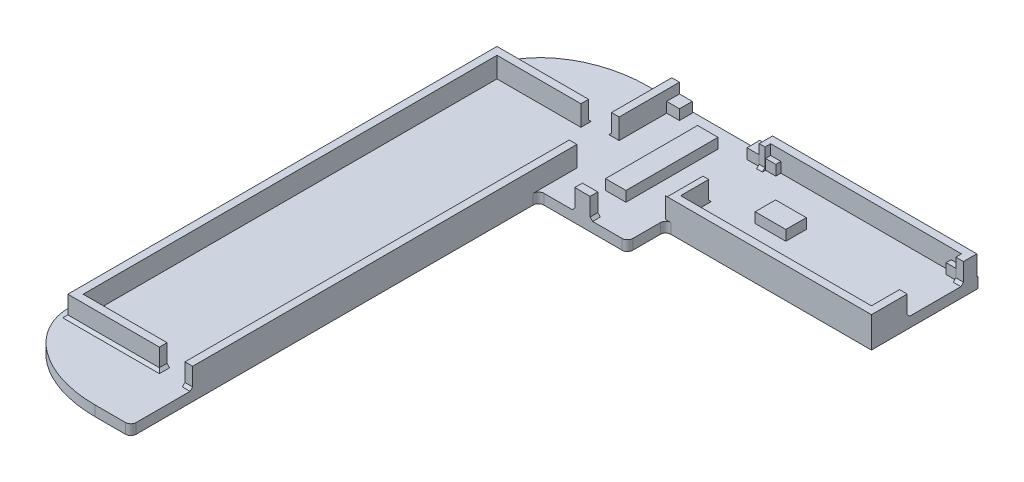
SolidWorks part; units mm, degrees
ref_plane "Front Plane" through (0, 0, 0) normal (0, 0, 1) x (1, 0, 0)
ref_plane "Top Plane" through (0, 0, 0) normal (0, 1, 0) x (1, 0, 0)
ref_plane "Right Plane" through (0, 0, 0) normal (1, 0, 0) x (0, 0, -1)
sketch "Sketch1" plane through (0, 0, 0) normal (0, 1, 0) x (1, 0, 0)
  line L0 (-57.0053, 40.4812) -> (-78.4053, 40.4812)
  line L1 (-78.4053, 40.4812) -> (-78.4053, -40.4188)
  line L2 (-78.4053, -40.4188) -> (-57.0053, -40.4188)
  line L3 (-57.0053, -40.4188) -> (-57.0053, 40.4812)
  line L4 (-78.1053, -40.1188) -> (-57.3053, -40.1188)
  line L5 (-57.3053, -40.1188) -> (-57.3053, 40.1812)
  line L6 (-57.3053, 40.1812) -> (-78.1053, 40.1812)
  line L7 (-78.1053, 40.1812) -> (-78.1053, -40.1188)
  line L8 (-78.1053, -40.1188) -> (-57.3053, -40.1188)
  line L9 (-57.3053, -40.1188) -> (-57.3053, 40.1812)
  line L10 (-57.3053, 40.1812) -> (-78.1053, 40.1812)
  line L11 (-78.1053, 40.1812) -> (-78.1053, -40.1188)
  line L12 (-55.5053, 41.9812) -> (-79.9053, 41.9812)
  line L13 (-79.9053, 41.9812) -> (-79.9053, -41.9188)
  line L14 (-79.9053, -41.9188) -> (-55.5053, -41.9188)
  line L15 (-55.5053, -41.9188) -> (-55.5053, 41.9812)
  line L16 (-56.0165, 54.3) -> (-56.0165, 33.2)
  line L17 (-48.4165, 27.2) -> (-45.4165, 27.2)
  line L18 (-37.8165, 33.2) -> (-37.8165, 40.1551)
  line L19 (-37.8165, 54.3) -> (-56.0165, 54.3)
  line L20 (-55.7165, 27.5) -> (-38.1165, 27.5)
  line L21 (-38.1165, 27.5) -> (-38.1165, 54)
  line L22 (-38.1165, 54) -> (-55.7165, 54)
  line L23 (-55.7165, 54) -> (-55.7165, 27.5)
  line L25 (-38.1165, 33.2) -> (-38.1165, 40.1551)
  line L26 (-38.1165, 54) -> (-55.7165, 54)
  line L27 (-55.7165, 54) -> (-55.7165, 33.2)
  line L28 (-36.3165, 55.8) -> (-57.5165, 55.8)
  line L29 (-57.5165, 55.8) -> (-57.5165, 33.2)
  line L30 (-48.4165, 25.7) -> (-45.4165, 25.7)
  line L31 (-36.3165, 33.2) -> (-36.3165, 34.9646)
  line L32 (-46.9165, 60.3419) -> (-46.9165, 21.4937) construction
  line L33 (-51.6665, 55.8) -> (-51.6665, 54.3)
  line L34 (-42.1665, 55.8) -> (-42.1665, 54.3)
  line L35 (0.6089, 52.2646) -> (-36.6911, 52.2646)
  line L36 (-36.6911, 52.2646) -> (-36.6911, 51.1551)
  line L37 (-36.6911, 34.6646) -> (0.6089, 34.6646)
  line L38 (0.6089, 34.6646) -> (0.6089, 40.1551)
  line L39 (0.3089, 34.9646) -> (0.3089, 51.9646)
  line L40 (0.3089, 51.9646) -> (-36.3911, 51.9646)
  line L41 (-36.3911, 51.9646) -> (-36.3911, 34.9646)
  line L42 (-36.3911, 34.9646) -> (0.3089, 34.9646)
  line L44 (0.3089, 51.9646) -> (-36.3911, 51.9646)
  line L46 (-36.3911, 34.9646) -> (0.3089, 34.9646)
  line L47 (2.1089, 53.7646) -> (-38.1911, 53.7646)
  line L48 (-38.1911, 53.7646) -> (-38.1911, 51.1551)
  line L49 (-38.1911, 33.1646) -> (2.1089, 33.1646)
  line L50 (2.1089, 33.1646) -> (2.1089, 40.1551)
  line L51 (0.6089, 51.1551) -> (2.1089, 51.1551)
  line L52 (7.7634, 45.6551) -> (-29.0417, 45.6551) construction
  line L53 (0.6089, 40.1551) -> (2.1089, 40.1551)
  line L54 (-18.0411, 53.7646) -> (-18.0411, 33.1646) construction
  line L55 (-36.6911, 40.1551) -> (-38.1911, 40.1551)
  line L56 (-36.6911, 51.1551) -> (-38.1911, 51.1551)
  line L57 (-57.5165, 33.2) -> (-36.3165, 33.2)
  line L58 (-48.4165, 27.2) -> (-48.4165, 25.7)
  line L59 (-45.4165, 27.2) -> (-45.4165, 25.7)
  line L60 (-55.7165, 54) -> (-55.7165, 27.5) construction
  line L61 (-56.0165, 54.3) -> (-56.0165, 27.2) construction
  line L62 (-57.5165, 55.8) -> (-57.5165, 25.7) construction
  line L63 (-55.7165, 27.5) -> (-38.1165, 27.5) construction
  line L64 (-56.0165, 27.2) -> (-37.8165, 27.2) construction
  line L65 (-57.5165, 25.7) -> (-36.3165, 25.7) construction
  line L66 (-38.1165, 27.5) -> (-38.1165, 54) construction
  line L67 (-37.8165, 27.2) -> (-37.8165, 54.3) construction
  line L68 (-36.3165, 25.7) -> (-36.3165, 55.8) construction
  line L69 (-36.3165, 51.9646) -> (-36.3165, 55.8)
  line L70 (-36.3911, 51.9646) -> (-36.3911, 34.9646) construction
  line L71 (-36.6911, 40.1551) -> (-36.6911, 34.6646)
  line L72 (-36.6911, 52.2646) -> (-36.6911, 34.6646) construction
  line L73 (-37.8165, 51.1551) -> (-37.8165, 54.3)
  line L74 (-38.1165, 51.1551) -> (-38.1165, 54)
  line L75 (-38.1911, 40.1551) -> (-38.1911, 33.1646)
  line L76 (-38.1911, 53.7646) -> (-38.1911, 33.1646) construction
  line L77 (2.1089, 51.1551) -> (2.1089, 53.7646)
  line L78 (2.1089, 33.1646) -> (2.1089, 53.7646) construction
  line L79 (0.6089, 51.1551) -> (0.6089, 52.2646)
  line L80 (0.6089, 34.6646) -> (0.6089, 52.2646) construction
  line L81 (0.3089, 34.9646) -> (0.3089, 51.9646) construction
  line L82 (-57.0053, -40.4188) -> (-57.0053, -41.9188)
  line L83 (-62.0053, -40.4188) -> (-62.0053, -41.9188)
  line L84 (-57.0053, 40.4812) -> (-57.0053, 41.9812)
  line L85 (-62.0053, 40.4812) -> (-62.0053, 41.9812)
  line L106 (-38.1911, 53.7646) -> (-57.5165, 53.7646)
  point P30 (-46.9165, 54.3)
  dimension "D7" = 9.5
  dimension "D11" = 11
  dimension "D12" = 3
  dimension "D13" = 6
  dimension "D14" = 5
  dimension "D15" = 5
  dimension "D1" = 0
  dimension "D2" = 0.3
  dimension "D3" = 1.5
  dimension "D4" = 0
  dimension "D5" = 0.3
  dimension "D6" = 1.5
  dimension "D8" = 0
  dimension "D9" = 0.3
  dimension "D10" = 1.5
extrude "Boss-Extrude1" add sketch "Sketch1" along normal blind 4 contours L0 L85 L12 L13 L14 L83 L2 L1 | L84 L3 L82 L14 L15 L12 | L73 L56 L36 L35 L69 L47 L48 L19 | L59 L17 L58 L30 | L53 L38 L37 L31 L49 L50 | L71 L55 L18 L49 L31 L37 | L79 L51 L77 L47 L69 L35 | L16 L106 L29 L57
sketch "Sketch2" plane through (0, 0, 0) normal (0, 1, 0) x (1, 0, 0)
  line L4 (2.1089, 54) -> (2.1089, 33.1646)
  line L5 (2.1089, 33.1646) -> (-37.0823, 33.1646)
  line L6 (-38.1911, 33.1646) -> (2.1089, 33.1646) construction
  line L7 (-38.1165, 32.1304) -> (-38.1165, 26.7342)
  line L8 (-39.1507, 25.7) -> (-54.4711, 25.7)
  line L9 (-55.5053, 24.6658) -> (-55.5053, -52.9658)
  line L10 (-56.5395, -54) -> (-62.5, -54)
  line L11 (-48.4165, 25.7) -> (-45.4165, 25.7) construction
  line L12 (-55.5053, -41.9188) -> (-55.5053, 33.2) construction
  line L13 (2.1089, 33.1646) -> (2.1089, 40.1551) construction
  line L14 (-38.1165, 27.5) -> (-38.1165, 54) construction
  line L15 (-81.5, -40) -> (-81.5, 40) construction
  line L16 (-62.5, 54) -> (62.5, 54) construction
  line L17 (-81.5, -40) -> (-81.5, 40)
  line L18 (-62.5, 54) -> (62.5, 54)
  arc A5 (-37.0823, 33.1646) -> (-38.1165, 32.1304) centre (-37.0823, 32.1304) ccw
  arc A6 (-38.1165, 26.7342) -> (-39.1507, 25.7) centre (-39.1507, 26.7342) cw
  arc A7 (-54.4711, 25.7) -> (-55.5053, 24.6658) centre (-54.4711, 24.6658) ccw
  arc A8 (-55.5053, -52.9658) -> (-56.5395, -54) centre (-56.5395, -52.9658) cw
  spline S0 degree 2 poles (906.6615, -113.4084) (-97.8488, -28.9763) (-81.0477, 43.1244) (-80.5493, 44.3985) (-80.0923, 45.2894) (-79.6622, 46.0036) (-79.231, 46.6299) (-78.6353, 47.4003) (-77.6996, 48.4208) (-76.6207, 49.3712) (-75.7771, 50.009) (-75.0407, 50.5107) (-74.3794, 50.9202) (-73.5063, 51.4143) (-72.2327, 52.0357) (-70.6947, 52.6436) (-69.043, 53.1551) (-67.4582, 53.5276) (40.3645, 71.4419) (369.5146, -847.8589) knots -5.619494 -5.619494 -5.619494 0.09375 0.15625 0.203125 0.234375 0.265625 0.296875 0.34375 0.40625 0.453125 0.484375 0.515625 0.546875 0.59375 0.65625 0.71875 0.78125 0.84375 9.070107 9.070107 9.070107 only from (-81.5, 40) to (-62.5, 54) construction
  spline S1 degree 2 poles (-81.5, 40) (-81.5022, 41.1738) (-81.0477, 43.1244) (-80.5493, 44.3985) (-80.0923, 45.2894) (-79.6622, 46.0036) (-79.231, 46.6299) (-78.6353, 47.4003) (-77.6996, 48.4208) (-76.6207, 49.3712) (-75.7771, 50.009) (-75.0407, 50.5107) (-74.3794, 50.9202) (-73.5063, 51.4143) (-72.2327, 52.0357) (-70.6947, 52.6436) (-69.043, 53.1551) (-67.4582, 53.5276) (-64.6127, 54.0004) (-62.5, 54) knots 0 0 0 0.09375 0.15625 0.203125 0.234375 0.265625 0.296875 0.34375 0.40625 0.453125 0.484375 0.515625 0.546875 0.59375 0.65625 0.71875 0.78125 0.84375 1 1 1
  spline S2 degree 2 poles (369.9801, 847.6429) (40.3498, -71.4914) (-67.4723, -53.5248) (-69.0638, -53.1494) (-70.7092, -52.6384) (-72.244, -52.0307) (-73.5148, -51.4097) (-74.3863, -50.916) (-75.0467, -50.5068) (-75.7813, -50.0059) (-76.6232, -49.3692) (-77.7002, -48.4201) (-78.6345, -47.4011) (-79.2303, -46.6306) (-79.6584, -46.0095) (-80.1051, -45.2692) (-80.5713, -44.3606) (-81.0729, -43.066) (-97.0833, 27.6838) (865.7865, 280.3768) knots -8.047224 -8.047224 -8.047224 0.15625 0.21875 0.28125 0.34375 0.40625 0.453125 0.484375 0.515625 0.546875 0.59375 0.65625 0.703125 0.734375 0.765625 0.796875 0.84375 0.90625 6.703951 6.703951 6.703951 only from (-62.5, -54) to (-81.5, -40) construction
  spline S3 degree 2 poles (-62.5, -54) (-64.6189, -54.0003) (-67.4723, -53.5248) (-69.0638, -53.1494) (-70.7092, -52.6384) (-72.244, -52.0307) (-73.5148, -51.4097) (-74.3863, -50.916) (-75.0467, -50.5068) (-75.7813, -50.0059) (-76.6232, -49.3692) (-77.7002, -48.4201) (-78.6345, -47.4011) (-79.2303, -46.6306) (-79.6584, -46.0095) (-80.1051, -45.2692) (-80.5713, -44.3606) (-81.0729, -43.066) (-81.4998, -41.1796) (-81.5, -40) knots 0 0 0 0.15625 0.21875 0.28125 0.34375 0.40625 0.453125 0.484375 0.515625 0.546875 0.59375 0.65625 0.703125 0.734375 0.765625 0.796875 0.84375 0.90625 1 1 1
  point P27 (-38.1165, 33.1646)
extrude "Boss-Extrude2" add sketch "Sketch2" against normal blind 2 contours S3 L10 A8 L9 A7 L8 A6 L7 A5 L5 L4 L18 S1 L17
sketch "Sketch5" plane through (0, 0, 0) normal (0, -1, 0) x (-1, 0, 0)
  line L0 (48.4165, 27.2) -> (45.4165, 27.2) construction
  line L1 (56.0165, 53.7646) -> (53.5165, 53.7646)
  line L2 (56.0165, 53.7646) -> (56.0165, 51.2646)
  line L3 (56.0165, 51.2646) -> (53.5165, 51.2646)
  line L4 (53.5165, 53.7646) -> (53.5165, 51.2646)
  line L5 (62.5, 54) -> (-2.1089, 54) construction
  line L6 (36.6911, 52.2646) -> (36.6911, 51.1551) construction
  line L11 (36.6911, 52.2646) -> (34.6911, 52.2646)
  line L12 (36.6911, 52.2646) -> (36.6911, 51.2646)
  line L13 (36.6911, 51.2646) -> (34.6911, 51.2646)
  line L14 (48.9165, 32.2) -> (44.9165, 32.2)
  line L15 (48.9165, 32.2) -> (48.9165, 50.2)
  line L16 (48.9165, 50.2) -> (44.9165, 50.2)
  line L17 (44.9165, 32.2) -> (44.9165, 50.2)
  line L18 (48.9165, 32.2) -> (44.9165, 50.2) construction
  line L19 (48.9165, 50.2) -> (44.9165, 32.2) construction
  line L20 (46.9165, 27.2) -> (46.9165, 54) construction
  line L21 (48.4165, 27.2) -> (45.4165, 27.2) construction
  line L22 (56.0165, 53.7646) -> (57.5165, 53.7646) construction
  line L23 (56.0165, 53.7646) -> (56.0165, 41.9812) construction
  line L24 (37.8165, 51.2646) -> (40.3165, 51.2646)
  line L25 (37.8165, 53.7646) -> (37.8165, 51.2646)
  line L26 (37.8165, 53.7646) -> (40.3165, 53.7646)
  line L27 (40.3165, 53.7646) -> (40.3165, 51.2646)
  line L28 (56.0165, 53.7646) -> (53.5165, 51.2646)
  line L29 (53.5165, 53.7646) -> (53.5165, 51.2646)
  line L30 (56.0165, 51.2646) -> (53.5165, 53.7646)
  line L31 (34.6911, 52.2646) -> (34.6911, 51.2646)
  line L33 (36.6911, 34.6646) -> (34.6911, 34.6646)
  line L34 (36.6911, 34.6646) -> (36.6911, 35.6646)
  line L35 (36.6911, 35.6646) -> (34.6911, 35.6646)
  line L36 (34.6911, 34.6646) -> (34.6911, 35.6646)
  line L37 (-0.6089, 52.2646) -> (1.3911, 52.2646)
  line L38 (-0.6089, 52.2646) -> (-0.6089, 51.2646)
  line L39 (-0.6089, 51.2646) -> (1.3911, 51.2646)
  line L40 (1.3911, 52.2646) -> (1.3911, 51.2646)
  line L41 (-0.6089, 34.6646) -> (1.3911, 34.6646)
  line L42 (-0.6089, 34.6646) -> (-0.6089, 35.6646)
  line L43 (-0.6089, 35.6646) -> (1.3911, 35.6646)
  line L44 (1.3911, 34.6646) -> (1.3911, 35.6646)
  line L45 (28.6853, 41.2263) -> (22.6853, 41.2263)
  line L46 (28.6853, 41.2263) -> (28.6853, 45.2263)
  line L47 (28.6853, 45.2263) -> (22.6853, 45.2263)
  line L48 (22.6853, 41.2263) -> (22.6853, 45.2263)
  line L49 (28.6853, 41.2263) -> (22.6853, 45.2263) construction
  line L50 (28.6853, 45.2263) -> (22.6853, 41.2263) construction
  point P18 (46.9165, 41.2)
  point P40 (25.6853, 43.2263)
  point P52 (25.6853, 43.2263)
  dimension "D1" = 2.5
  dimension "D2" = 2.5
  dimension "D3" = 5
  dimension "D4" = 2
  dimension "D5" = 4
  dimension "D6" = 18
  dimension "D7" = 1
  dimension "D8" = 2
  dimension "D9" = 1
  dimension "D10" = 2
  dimension "D11" = 1
  dimension "D12" = 2
  dimension "D13" = 1
  dimension "D14" = 6
  dimension "D15" = 4
extrude "Boss-Extrude3" add sketch "Sketch5" against normal blind 2
chamfer "Chamfer1" distance 0.5 angle 45 12 edges at (-37.2538, 0, -40.1551) (-37.2538, 0, -51.1551) (1.3589, 0, -40.1551) (1.3589, 0, -51.1551) (-45.4165, 0, -26.45) (-48.4165, 0, -26.45) (-56.2553, 0, 41.9188) (-57.5165, 0, -47.8729) (-62.0053, 0, 41.1688) (-70.9553, 0, 41.9188) (-79.9053, 0, -0.0312) (-70.9553, 0, -41.9812)
